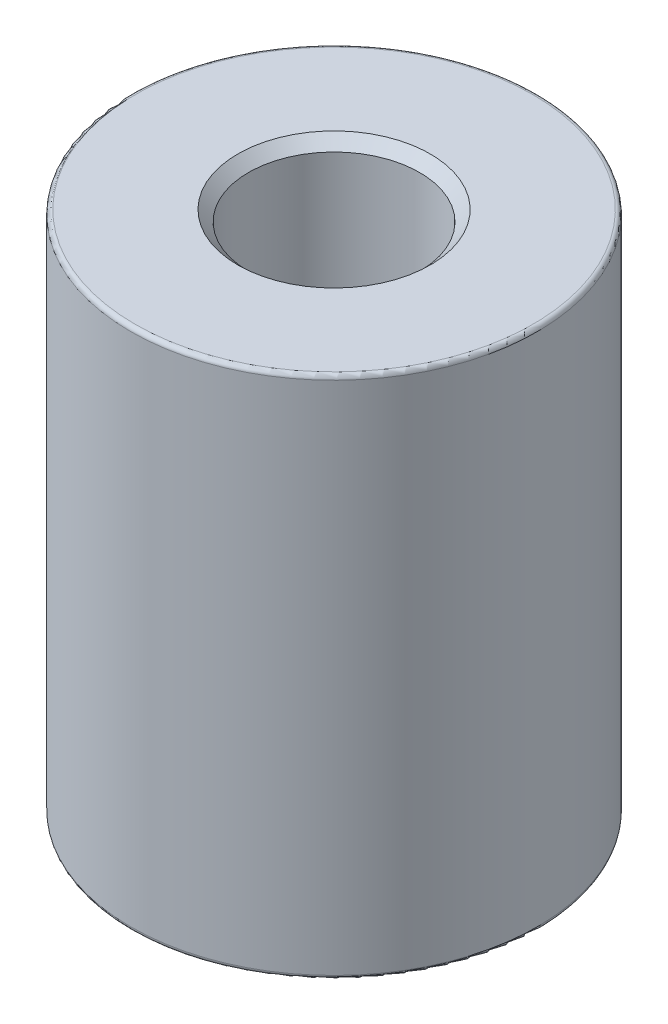
SolidWorks part; units mm, degrees
ref_plane "Front" through (0, 0, 0) normal (0, 0, 1) x (1, 0, 0)
ref_plane "Top" through (0, 0, 0) normal (0, 1, 0) x (1, 0, 0)
ref_plane "Right" through (0, 0, 0) normal (1, 0, 0) x (0, 0, -1)
sketch "草图1" plane through (0, 0, 0) normal (0, 1, 0) x (1, 0, 0)
  circle A0 centre (0, 0) radius 9.5
  dimension "D1" = 19
extrude "凸台-拉伸1" add sketch "草图1" along normal blind 24.5
sketch "草图2" plane through (0, 24.5, 0) normal (0, 1, 0) x (1, 0, 0)
  circle A0 centre (0, 0) radius 4
  dimension "D1" = 8
extrude "切除-拉伸1" cut sketch "草图2" against normal blind 16
sketch "草图3" plane through (0, 0, 0) normal (0, -1, 0) x (1, 0, 0)
  circle A0 centre (0, 0) radius 3
  dimension "D1" = 6
extrude "切除-拉伸2" cut sketch "草图3" against normal blind 16
chamfer "倒角1" distance 0.5 angle 45 2 edges at (0, 24.5, 4) (0, 0, -3)
fillet "圆角1" radius 0.2 2 edges at (0, 24.5, 9.5) (0, 0, 9.5)
